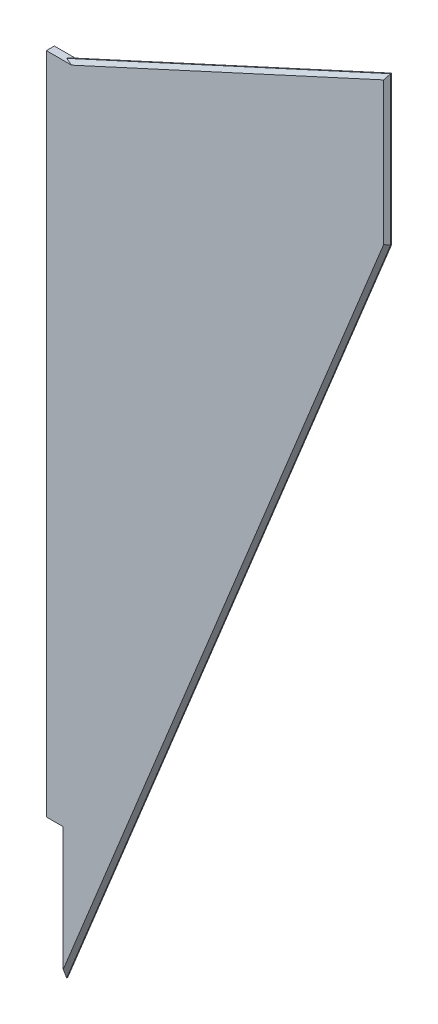
SolidWorks part; units mm, degrees
ref_plane "Front Plane" through (0, 0, 0) normal (0, 0, 1) x (1, 0, 0)
ref_plane "Top Plane" through (0, 0, 0) normal (0, 1, 0) x (1, 0, 0)
ref_plane "Right Plane" through (0, 0, 0) normal (1, 0, 0) x (0, 0, -1)
sketch "Sketch1" plane through (0, 0, 0) normal (0, 0, 1) x (1, 0, 0)
  line L15 (60, 2660) -> (59.9812, 2660)
  line L16 (59.9812, 2660) -> (59.9812, 2359.9539)
  line L17 (59.9812, 2359.9539) -> (182, 2660)
  line L18 (182, 2660) -> (182, 2716)
  line L19 (182, 2716) -> (60, 2660)
extrude "Boss-Extrude1" add sketch "Sketch1" along normal blind 3
sketch "Sketch2" plane through (59.9812, 0, 0) normal (-1, 0, 0) x (0, 0, 1)
  line L0 (0, 2660) -> (0, 2359.9539) construction
  line L1 (0, 2409.9539) -> (3, 2409.9539)
  line L2 (0, 2409.9539) -> (0, 2660)
  line L3 (0, 2660) -> (3, 2660)
  line L4 (3, 2409.9539) -> (3, 2660)
  line L5 (3, 2359.9539) -> (0, 2359.9539) construction
  point P9 (1.5, 2359.9539)
  dimension "D1" = 50
extrude "Boss-Extrude2" add sketch "Sketch2" along normal blind 6.35
chamfer "Chamfer1" distance 1.3 angle 45 2 edges at (120.9906, 2509.9769, 0) (120.9906, 2509.9769, 3)
chamfer "Chamfer2" distance 1.3 angle 45 2 edges at (121, 2688, 0) (121, 2688, 3)
chamfer "Chamfer3" distance 1.3 angle 45 2 edges at (182, 2689.0103, 0) (182, 2689.0103, 3)
